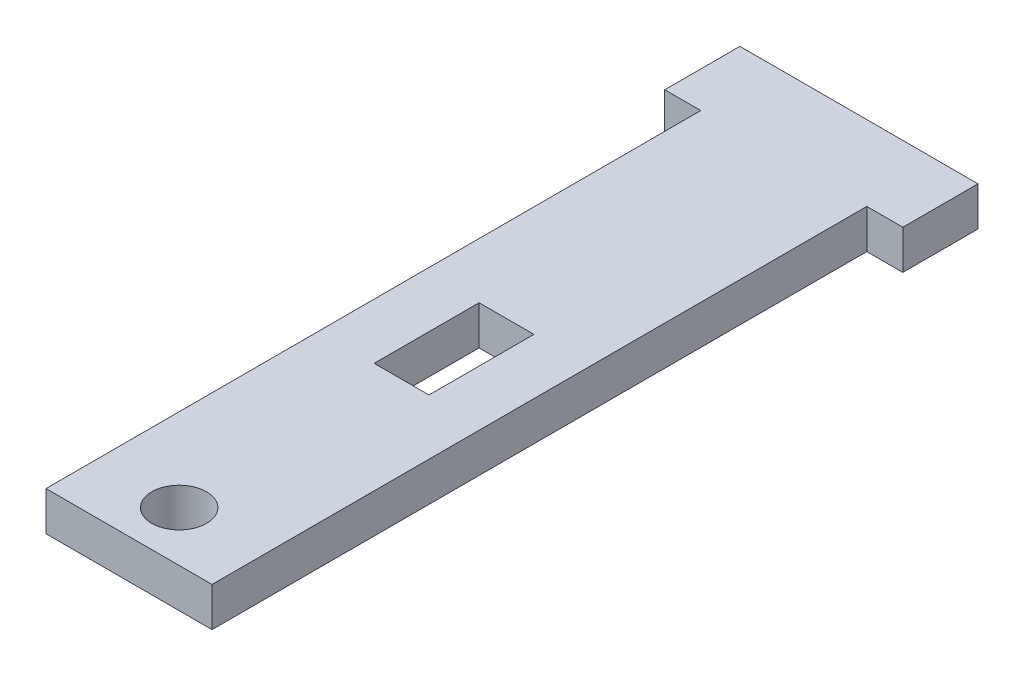
SolidWorks part; units mm, degrees
material "PLA"
ref_plane "Front Plane" through (0, 0, 0) normal (0, 0, 1) x (1, 0, 0)
ref_plane "Top Plane" through (0, 0, 0) normal (0, 1, 0) x (1, 0, 0)
ref_plane "Right Plane" through (0, 0, 0) normal (1, 0, 0) x (0, 0, -1)
sketch "Sketch1" plane through (0, 0, 0) normal (0, 1, 0) x (1, 0, 0)
  line L0 (0, 0) -> (0, 37.7494) construction
  line L1 (5.3, 0) -> (-5.3, 0)
  line L2 (-5.3, 0) -> (-5.3, 41.8)
  line L3 (-5.3, 41.8) -> (-7.6, 41.8)
  line L4 (-7.6, 41.8) -> (-7.6, 46.6)
  line L5 (-7.6, 46.6) -> (7.6, 46.6)
  line L6 (7.6, 41.8) -> (7.6, 46.6)
  line L7 (5.3, 41.8) -> (7.6, 41.8)
  line L8 (5.3, 0) -> (5.3, 41.8)
  point P9 (0, 46.6)
  dimension "D1" = 5.3
  dimension "D2" = 41.8
  dimension "D3" = 2.3
  dimension "D4" = 4.8
sketch "Sketch2" plane through (0, 0, 0) normal (0, 1, 0) x (1, 0, 0)
  line L0 (0, 0) -> (0, 37.7494) construction
  line L1 (-7.6, 46.6) -> (7.6, 46.6) construction
  line L2 (-1.75, 24.1) -> (1.75, 24.1)
  line L3 (-1.75, 24.1) -> (-1.75, 17.4)
  line L4 (-1.75, 17.4) -> (1.75, 17.4)
  line L5 (1.75, 24.1) -> (1.75, 17.4)
  line L6 (-1.75, 24.1) -> (1.75, 17.4) construction
  line L7 (-1.75, 17.4) -> (1.75, 24.1) construction
  circle A0 centre (0, 3.2) radius 1.75
  point P4 (0, 20.75)
  dimension "D1" = 3.5
  dimension "D2" = 3.2
  dimension "D3" = 3.5
  dimension "D4" = 6.7
  dimension "D5" = 22.5
extrude "Boss-Extrude1" add sketch "Sketch1" along normal blind 2.5
extrude "Cut-Extrude1" cut sketch "Sketch2" along normal blind 2.5
